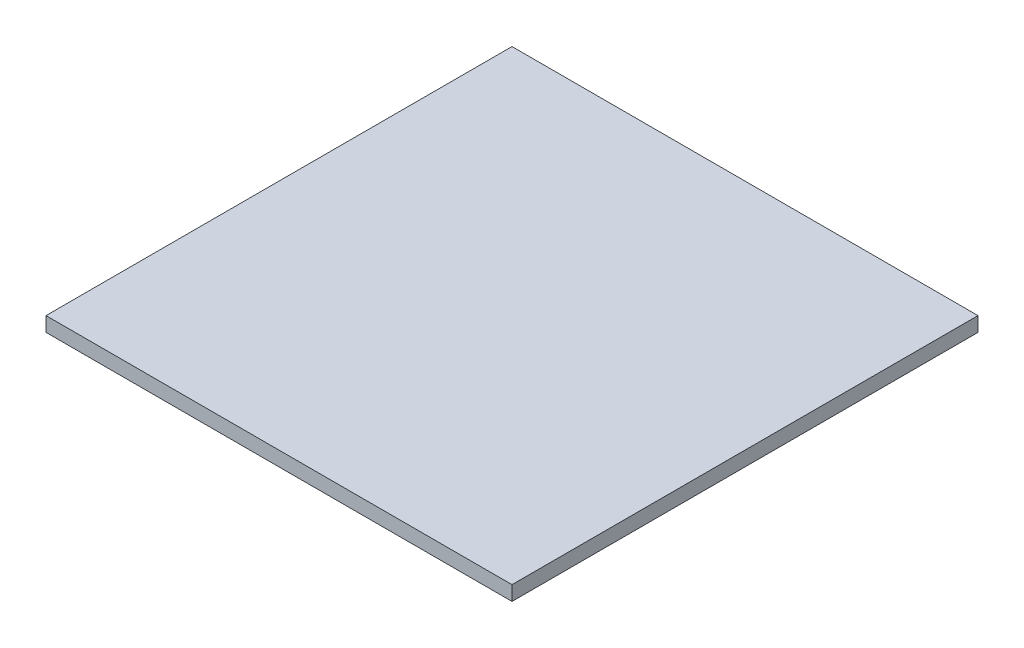
SolidWorks part; units mm, degrees
ref_plane "Front Plane" through (0, 0, 0) normal (0, 0, 1) x (1, 0, 0)
ref_plane "Top Plane" through (0, 0, 0) normal (0, 1, 0) x (1, 0, 0)
ref_plane "Right Plane" through (0, 0, 0) normal (1, 0, 0) x (0, 0, -1)
sketch "Sketch2" plane through (0, 0, 0) normal (0, 1, 0) x (1, 0, 0)
  line L0 (0, 0) -> (-64, 0)
  line L1 (-64, 0) -> (-64, -64)
  line L2 (-64, -64) -> (0, -64)
  line L3 (0, -64) -> (0, 0)
  dimension "D1" = 64
  dimension "D2" = 64
extrude "Boss-Extrude1" add sketch "Sketch2" along normal blind 2
